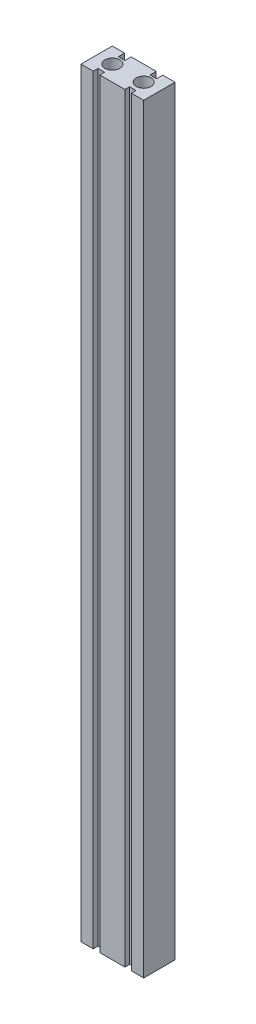
SolidWorks part; units mm, degrees
ref_plane "前视基准面" through (0, 0, 0) normal (0, 0, 1) x (1, 0, 0)
ref_plane "上视基准面" through (0, 0, 0) normal (0, 1, 0) x (1, 0, 0)
ref_plane "右视基准面" through (0, 0, 0) normal (1, 0, 0) x (0, 0, -1)
sketch "草图2" plane through (0, 0, 0) normal (0, 1, 0) x (1, 0, 0)
  line L1 (-20, 10) -> (20, 10)
  line L2 (-20, 10) -> (-20, -10)
  line L3 (-20, -10) -> (20, -10)
  line L4 (20, 10) -> (20, -10)
  line L5 (-20, 10) -> (20, -10) construction
  line L6 (-20, -10) -> (20, 10) construction
  point P0 (0, 0)
  dimension "D1" = 40
  dimension "D2" = 20
extrude "凸台-拉伸1" add sketch "草图2" along normal blind 485
sketch "草图3" plane through (0, 0, 0) normal (0, -1, 0) x (1, 0, 0)
  line L0 (0, 0) -> (0, -14.1253) construction
  line L2 (20, -10) -> (-20, -10) construction
  circle A0 centre (-10, 0) radius 4.75
  circle A1 centre (10, 0) radius 4.75
  dimension "D2" = 9.5
  dimension "D1" = 20
  dimension "D3" = 10
extrude "切除-拉伸1" cut sketch "草图3" against normal through all
sketch "草图4" plane through (0, 0, 10) normal (0, 0, 1) x (1, 0, 0)
  line L0 (0, 0) -> (0, 202.505) construction
  line L1 (-20, 0) -> (20, 0) construction
  line L2 (-12.2, 0) -> (-8, 0)
  line L3 (-12.2, 0) -> (-12.2, 485)
  line L4 (-12.2, 485) -> (-8, 485)
  line L5 (-8, 0) -> (-8, 485)
  line L6 (-20, 485) -> (20, 485) construction
  line L7 (12.2, 0) -> (8, 0)
  line L8 (12.2, 485) -> (8, 485)
  line L9 (8, 0) -> (8, 485)
  line L10 (12.2, 0) -> (12.2, 485)
  dimension "D1" = 4.2
  dimension "D2" = 16
extrude "切除-拉伸2" cut sketch "草图4" against normal blind 3
sketch "草图5" plane through (0, 0, -10) normal (0, 0, -1) x (-1, 0, 0)
  line L4 (-12.2, 0) -> (-8, 0)
  line L5 (-8, 0) -> (-8, 485)
  line L6 (-8, 485) -> (-12.2, 485)
  line L7 (-12.2, 485) -> (-12.2, 0)
  line L8 (-12.2, 0) -> (-8, 0)
  line L9 (-8, 0) -> (-8, 485)
  line L10 (-8, 485) -> (-12.2, 485)
  line L11 (-12.2, 485) -> (-12.2, 0)
  line L12 (8, 0) -> (12.2, 0)
  line L13 (8, 485) -> (8, 0)
  line L14 (12.2, 485) -> (8, 485)
  line L15 (12.2, 0) -> (12.2, 485)
  line L16 (8, 0) -> (12.2, 0)
  line L17 (8, 485) -> (8, 0)
  line L18 (12.2, 485) -> (8, 485)
  line L19 (12.2, 0) -> (12.2, 485)
  dimension "D1" = 0
  dimension "D2" = 0
extrude "切除-拉伸3" cut sketch "草图5" against normal blind 4
